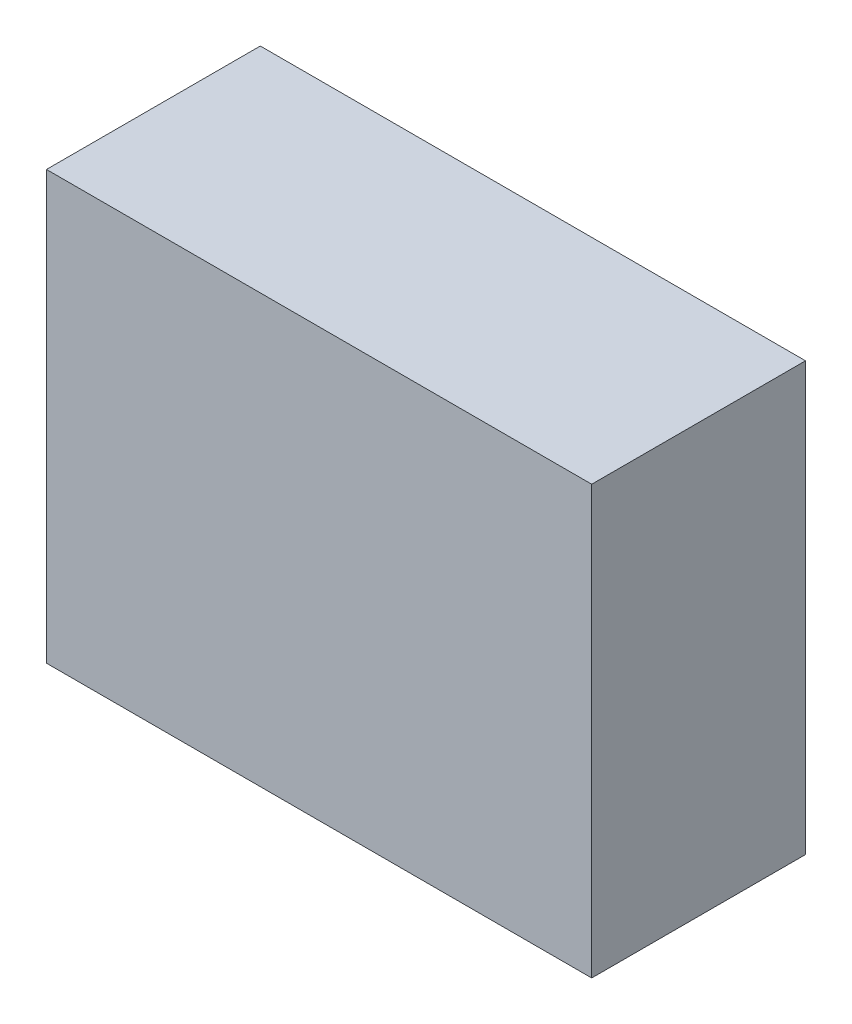
SolidWorks part; units mm, degrees
ref_plane "Plan de face" through (0, 0, 0) normal (0, 0, 1) x (1, 0, 0)
ref_plane "Plan de dessus" through (0, 0, 0) normal (0, 1, 0) x (1, 0, 0)
ref_plane "Plan de droite" through (0, 0, 0) normal (1, 0, 0) x (0, 0, -1)
sketch "Esquisse1" plane through (0, 0, 0) normal (0, 0, 1) x (1, 0, 0)
  line L1 (0, 0) -> (51, 0)
  line L2 (0, 0) -> (0, 40)
  line L3 (0, 40) -> (51, 40)
  line L4 (51, 0) -> (51, 40)
  dimension "D1" = 51
  dimension "D2" = 40
extrude "Boss.-Extru.1" add sketch "Esquisse1" along normal blind 20
